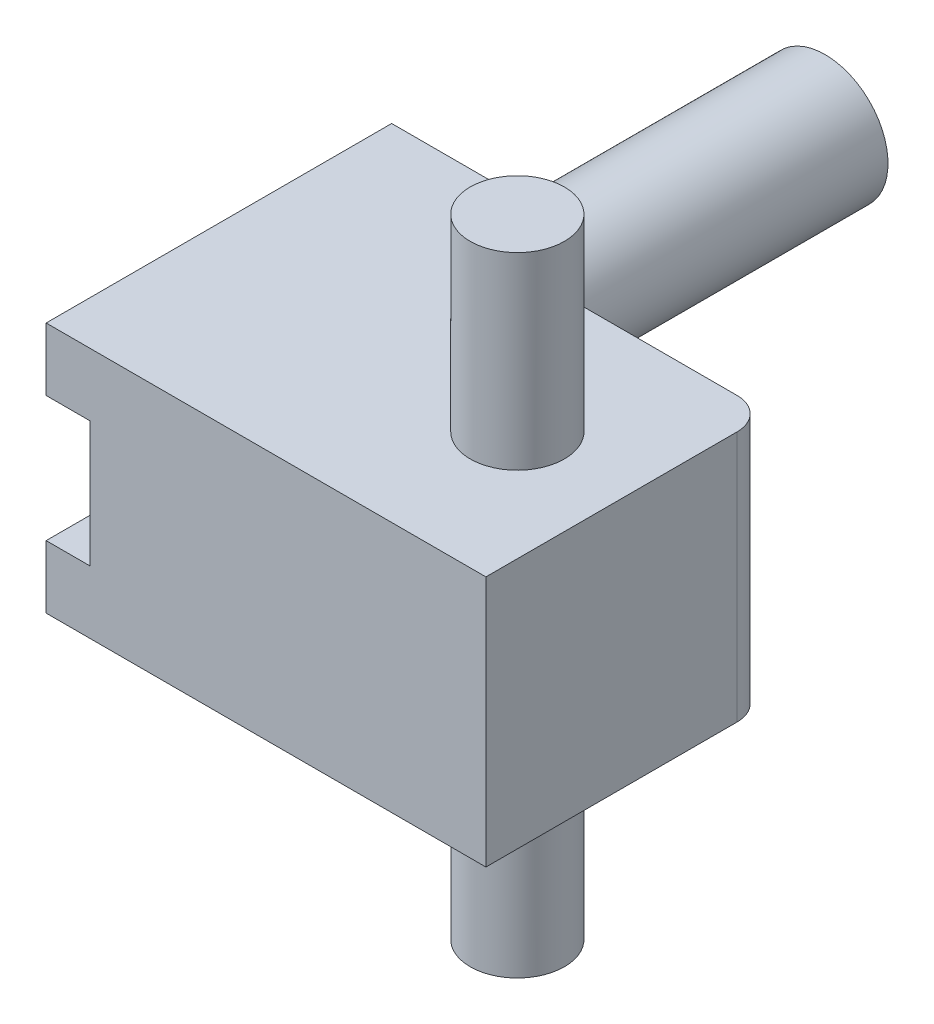
SolidWorks part; units mm, degrees
ref_plane "Alzado" through (0, 0, 0) normal (0, 0, 1) x (1, 0, 0)
ref_plane "Planta" through (0, 0, 0) normal (0, 1, 0) x (1, 0, 0)
ref_plane "Vista lateral" through (0, 0, 0) normal (1, 0, 0) x (0, 0, -1)
sketch "Croquis2" plane through (0, 0, 0) normal (0, 0, 1) x (1, 0, 0)
  line L0 (0, 0) -> (0, 40)
  line L1 (0, 40) -> (70, 40)
  line L2 (70, 40) -> (70, 0)
  line L3 (70, 0) -> (0, 0)
  dimension "D1" = 40
  dimension "D2" = 70
extrude "Saliente-Extruir1" add sketch "Croquis2" along normal blind 45
sketch "Croquis3" plane through (0, 0, 0) normal (0, 0, -1) x (-1, 0, 0)
  line L0 (0, 0) -> (0, 10)
  line L1 (0, 40) -> (0, 0) construction
  line L2 (0, 10) -> (0, 30)
  line L3 (0, 30) -> (0, 40)
  line L4 (0, 10) -> (-70, 10)
  line L5 (-70, 0) -> (-70, 40) construction
  line L6 (-70, 10) -> (-70, 30)
  line L8 (0, 30) -> (-7, 30)
  line L9 (-7, 30) -> (-7, 10)
  line L10 (-7, 10) -> (-47.5, 10)
  line L11 (-7, 10) -> (-7, 30)
  line L12 (-7, 30) -> (-47.5, 30)
  line L13 (-47.5, 10) -> (-47.5, 30)
  dimension "D1" = 10
  dimension "D2" = 10
  dimension "D3" = 7
  dimension "D4" = 40.5
extrude "Cortar-Extruir1" cut sketch "Croquis3" against normal blind 39 contours L13 L4 L9 L12
sketch "Croquis4" plane through (0, 0, 0) normal (0, 0, -1) x (-1, 0, 0)
  line L0 (-7, 10) -> (0, 10)
  line L1 (0, 40) -> (0, 0) construction
  line L2 (0, 10) -> (0, 30)
  line L3 (0, 30) -> (-7, 30)
  line L4 (-7, 30) -> (-7, 10)
  line L6 (-47.5, 10) -> (-54.5, 10)
  line L7 (-47.5, 10) -> (-47.5, 30)
  line L8 (-47.5, 30) -> (-54.5, 30)
  line L9 (-54.5, 10) -> (-54.5, 30)
  dimension "D1" = 7
extrude "Cortar-Extruir2" cut sketch "Croquis4" against normal blind 12 contours L4 L0 L2 L3 | L7 L6 L9 L8
sketch "Croquis5" plane through (0, 0, 0) normal (-1, 0, 0) x (0, 0, 1)
  line L0 (25, 10) -> (25, 30)
  line L1 (25, 10) -> (45, 10)
  line L2 (45, 40) -> (45, 0) construction
  line L3 (45, 10) -> (45, 30)
  line L4 (45, 30) -> (25, 30)
  dimension "D1" = 20
extrude "Cortar-Extruir4" cut sketch "Croquis5" against normal blind 7
sketch "Croquis6" plane through (0, 40, 0) normal (0, 1, 0) x (1, 0, 0)
  line L0 (70, 0) -> (0, 0) construction
  line L1 (70, -45) -> (35, -45) construction
  line L2 (70, -45) -> (70, 0) construction
  line L3 (70, 0) -> (35, 0) construction
  line L4 (35, -45) -> (35, 0) construction
  line L5 (35, 0) -> (70, -45) construction
  circle A0 centre (52.5, -22.5) radius 7.5
  dimension "D1" = 15
  dimension "D2" = 35
extrude "Saliente-Extruir3" add sketch "Croquis6" along normal blind 30
sketch "Croquis8" plane through (0, 0, 0) normal (0, -1, 0) x (1, 0, 0)
  line L0 (0, 0) -> (70, 0) construction
  line L1 (70, 45) -> (35, 45) construction
  line L2 (70, 45) -> (70, 0) construction
  line L3 (70, 0) -> (35, 0) construction
  line L4 (35, 45) -> (35, 0) construction
  line L5 (70, 45) -> (35, 0) construction
  circle A0 centre (52.5, 22.5) radius 7.5
  dimension "D2" = 15
  dimension "D1" = 35
extrude "Saliente-Extruir4" add sketch "Croquis8" along normal blind 30
sketch "Croquis9" plane through (0, 0, 0) normal (0, 0, -1) x (-1, 0, 0)
  line L0 (0, 40) -> (-30, 40)
  line L1 (-70, 40) -> (0, 40) construction
  line L2 (-30, 40) -> (-30, 0)
  line L3 (0, 0) -> (-70, 0) construction
  line L4 (-30, 0) -> (0, 0)
  line L5 (0, 0) -> (0, 40)
  dimension "D1" = 30
extrude "Saliente-Extruir5" add sketch "Croquis9" along normal blind 10
sketch "Croquis10" plane through (0, 0, -10) normal (0, 0, -1) x (-1, 0, 0)
  line L0 (-30, 0) -> (0, 40) construction
  circle A0 centre (-15, 20) radius 10
  dimension "D1" = 20
extrude "Saliente-Extruir6" add sketch "Croquis10" along normal blind 54
fillet "Redondeo1" radius 5 1 edges at (70, 20, 0)
